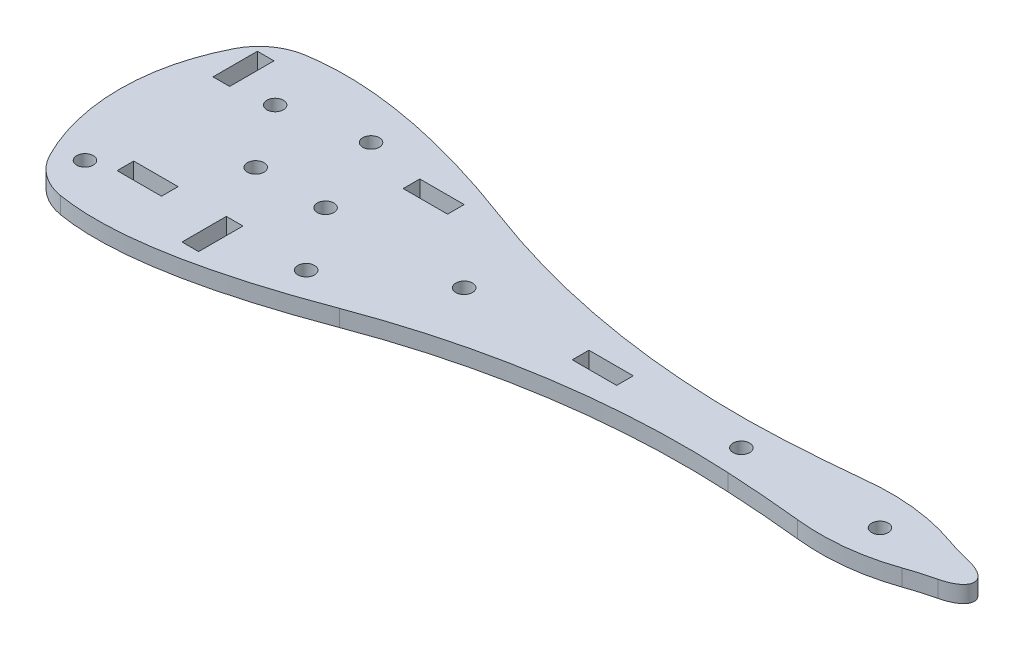
SolidWorks part; units mm, degrees
ref_plane "Plano frontal" through (0, 0, 0) normal (0, 0, 1) x (1, 0, 0)
ref_plane "Plano superior" through (0, 0, 0) normal (0, 1, 0) x (1, 0, 0)
ref_plane "Plano direito" through (0, 0, 0) normal (1, 0, 0) x (0, 0, -1)
sketch "Esboço1" plane through (0, 0, 0) normal (0, 1, 0) x (1, 0, 0)
  line L96 (-1.3, -10.3) -> (1.7, -10.3)
  line L97 (1.7, -10.3) -> (1.7, -18.3)
  line L98 (1.7, -18.3) -> (-1.3, -18.3)
  line L99 (-1.3, -18.3) -> (-1.3, -10.3)
  line L100 (-21.3, 10.3) -> (-24.3, 10.3)
  line L101 (-24.3, 10.3) -> (-24.3, 18.3)
  line L102 (-24.3, 18.3) -> (-21.3, 18.3)
  line L103 (-21.3, 18.3) -> (-21.3, 10.3)
  line L104 (10.3, 10) -> (10.3, 13)
  line L105 (10.3, 13) -> (18.3, 13)
  line L106 (18.3, 13) -> (18.3, 10)
  line L107 (18.3, 10) -> (10.3, 10)
  line L108 (-10.3, -10) -> (-10.3, -13)
  line L109 (-10.3, -13) -> (-18.3, -13)
  line L110 (-18.3, -13) -> (-18.3, -10)
  line L111 (-18.3, -10) -> (-10.3, -10)
  line L112 (56.3, -1.5) -> (60.3, -1.5)
  line L113 (60.3, -1.5) -> (60.3, 1.5)
  line L114 (60.3, 1.5) -> (52.3, 1.5)
  line L115 (52.3, 1.5) -> (52.3, -1.5)
  line L116 (52.3, -1.5) -> (56.3, -1.5)
  circle A10 centre (0.2, 14.3) radius 1.5
  circle A11 centre (-22.8, -14.3) radius 1.5
  circle A12 centre (-14.3, 11.5) radius 1.5
  circle A13 centre (14.3, -11.5) radius 1.5
  arc A24 (-26.7508, 16.7197) -> (-26.7508, -16.7197) centre (5.6027, 0) ccw
  arc A25 (-26.7508, 16.7197) -> (-19.544, 21.9871) centre (-17.8669, 12.1287) cw
  arc A26 (-26.7508, -16.7197) -> (-19.544, -21.9871) centre (-17.8669, -12.1287) ccw
  arc A27 (23.2473, 14.4669) -> (83.9533, 5.0794) centre (76.0379, 154.8705) ccw
  arc A28 (23.2473, -14.4669) -> (83.9533, -5.0794) centre (76.0379, -154.8705) cw
  arc A29 (119.5432, 2.8071) -> (114.5697, 4.2595) centre (131.0539, 51.464) cw
  arc A30 (114.5697, -4.2595) -> (119.5432, -2.8071) centre (131.0539, -51.464) cw
  circle A31 centre (6.3, 0) radius 1.5
  circle A32 centre (106.3, 0) radius 1.5
  circle A33 centre (81.3, 0) radius 1.5
  circle A35 centre (31.3, 0) radius 1.5
  circle A38 centre (-6.3, 0) radius 1.5
  ellipse E0 centre (116.3, 0) end of major axis (123.3, 0) minor radius 3.1675 (119.5432, -2.8071) -> (119.5432, 2.8071) ccw
  spline S0 degree 3 poles (114.5697, 4.2595) (109.1349, 6.1573) (103.4778, 6.7875) (97.5985, 6.15) knots 0.353889 0.353889 0.353889 0.353889 1 1 1 1
  spline S1 degree 3 poles (97.5985, 6.15) (93.039, 5.6761) (88.4906, 5.3192) (83.9533, 5.0794) knots 0 0 0 0 0.13796 0.13796 0.13796 0.13796
  spline S2 degree 3 poles (23.2473, 14.4669) (22.2154, 14.8549) (7.8436, 20.1288) (-8.0325, 23.9454) (-19.544, 21.9871) knots 0.189497 0.189497 0.189497 0.189497 0.21644 0.561127 0.561127 0.561127 0.561127
  spline S3 degree 3 poles (23.2473, -14.4669) (22.2154, -14.8549) (7.8436, -20.1288) (-8.0325, -23.9454) (-19.544, -21.9871) knots 0.189497 0.189497 0.189497 0.189497 0.21644 0.561127 0.561127 0.561127 0.561127
  spline S4 degree 3 poles (97.5985, -6.15) (93.039, -5.6761) (88.4906, -5.3192) (83.9533, -5.0794) knots 0 0 0 0 0.13796 0.13796 0.13796 0.13796
  spline S5 degree 3 poles (114.5697, -4.2595) (109.1349, -6.1573) (103.4778, -6.7875) (97.5985, -6.15) knots 0.353889 0.353889 0.353889 0.353889 1 1 1 1
  dimension "D1" = 10
  dimension "D2" = 10
extrude "Ressalto-extrusão1" add sketch "Esboço1" along normal blind 3
